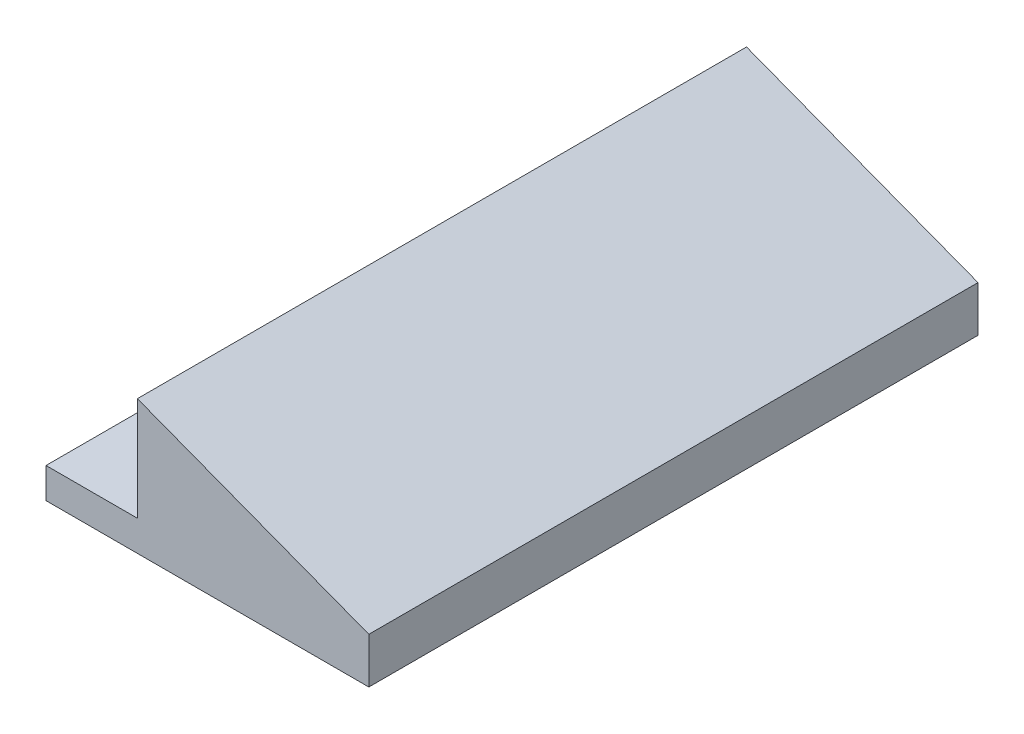
SolidWorks part; units mm, degrees
ref_plane "Front Plane" through (0, 0, 0) normal (0, 0, 1) x (1, 0, 0)
ref_plane "Top Plane" through (0, 0, 0) normal (0, 1, 0) x (1, 0, 0)
ref_plane "Right Plane" through (0, 0, 0) normal (1, 0, 0) x (0, 0, -1)
sketch "Croquis1" plane through (0, 0, 0) normal (0, 0, 1) x (1, 0, 0)
  line L0 (0, 0) -> (-15, 0)
  line L1 (-15, 0) -> (-15, 5)
  line L2 (-15, 5) -> (0, 5)
  line L3 (0, 5) -> (0, 22)
  line L5 (38, 0) -> (0, 0)
  line L6 (38, 0) -> (38, 7.5)
  line L7 (0, 22) -> (38, 7.5)
  dimension "D1" = 22
  dimension "D2" = 38
  dimension "D3" = 5
  dimension "D4" = 15
  dimension "D5" = 7.5
extrude "Saliente-Extruir1" add sketch "Croquis1" along normal blind 100
sketch "Croquis2" plane through (0, 5, 0) normal (0, 1, 0) x (1, 0, 0)
  line L0 (0, -100) -> (-15, -100) construction
  line L1 (0, 0) -> (-15, 0) construction
  line L2 (-15, -100) -> (-15, 0) construction
  circle A0 centre (-7.5, -80) radius 2
  circle A1 centre (-7.5, -20) radius 2
  dimension "D1" = 4
  dimension "D2" = 4
  dimension "D3" = 20
  dimension "D4" = 20
  dimension "D5" = 7.5
  dimension "D6" = 7.5
extrude "Cortar-Extruir1" cut sketch "Croquis2" against normal blind 100
